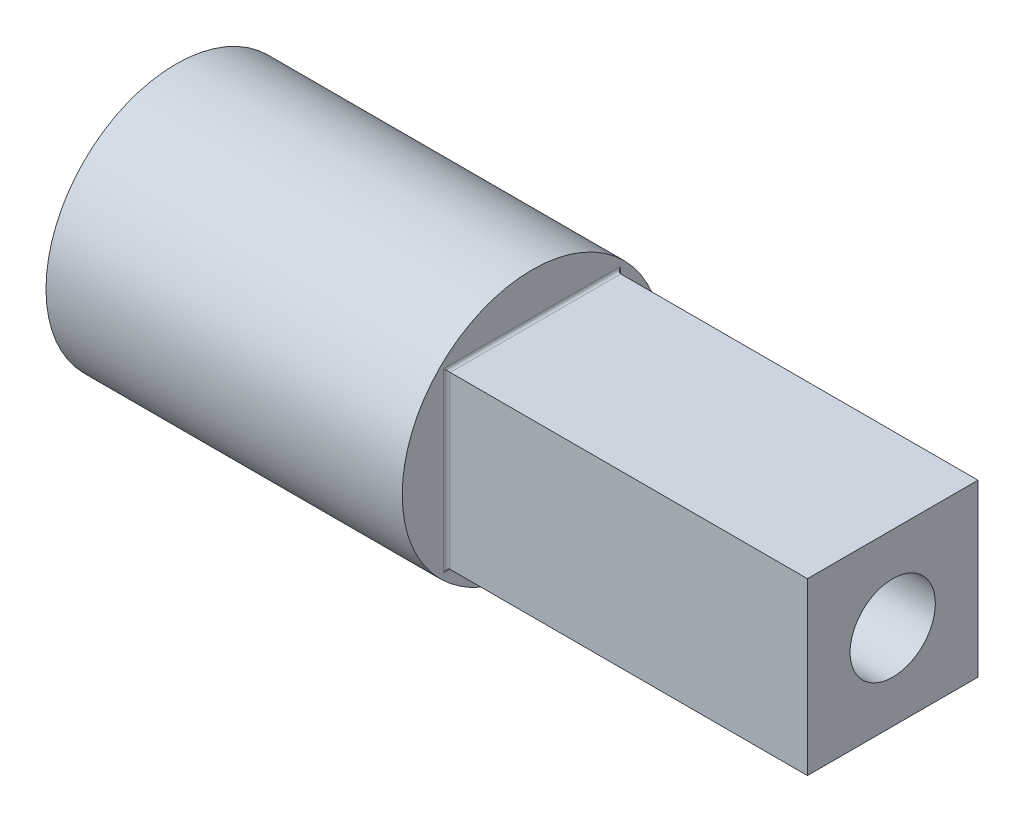
SolidWorks part; units mm, degrees
ref_plane "Front Plane" through (0, 0, 0) normal (0, 0, 1) x (1, 0, 0)
ref_plane "Top Plane" through (0, 0, 0) normal (0, 1, 0) x (1, 0, 0)
ref_plane "Right Plane" through (0, 0, 0) normal (1, 0, 0) x (0, 0, -1)
sketch "Sketch1" plane through (0, 0, 0) normal (1, 0, 0) x (0, 0, -1)
  circle A0 centre (0, 0) radius 32
  dimension "D1" = 64
extrude "Boss-Extrude1" add sketch "Sketch1" along normal blind 87.72 contours A0
sketch "Sketch2" plane through (87.72, 0, 0) normal (1, 0, 0) x (0, 0, -1)
  line L0 (-21, 21) -> (-21, -21)
  line L6 (21, 21) -> (21, -21)
  line L12 (-21, 0) -> (21, 0) construction
  line L13 (-21, -21) -> (21, -21)
  line L14 (-21, 21) -> (21, 21)
  point P14 (0, 0)
  dimension "D1" = 42
  dimension "D2" = 42
extrude "Boss-Extrude2" add sketch "Sketch2" along normal blind 88.78
fillet "Fillet2" radius 0.8 4 edges at (87.72, 0, 21) (87.72, 0, -21) (87.72, -21, 0) (87.72, 21, 0)
sketch "Sketch3" plane through (176.5, 0, 0) normal (1, 0, 0) x (0, 0, -1)
  circle A0 centre (0, 0) radius 10.5
  dimension "D1" = 21
extrude "Cut-Extrude1" cut sketch "Sketch3" against normal blind 16
